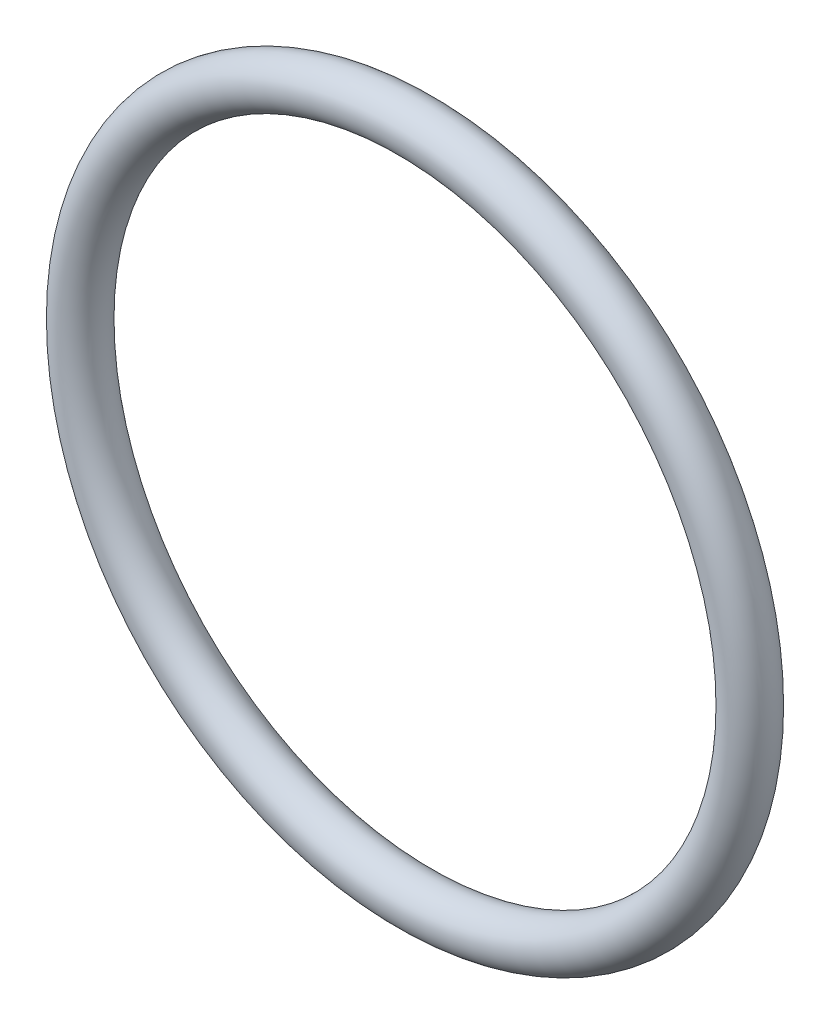
SolidWorks part; units mm, degrees
ref_plane "Plan de face" through (0, 0, 0) normal (0, 0, 1) x (1, 0, 0)
ref_plane "Plan de dessus" through (0, 0, 0) normal (0, 1, 0) x (1, 0, 0)
ref_plane "Plan de droite" through (0, 0, 0) normal (1, 0, 0) x (0, 0, -1)
ref_axis "Axe1" through (0, 0, -88.99) along (0, 0, 1)
sketch "Esquisse1" plane through (0, 0, 0) normal (1, 0, 0) x (0, 0, -1)
  line L0 (0, 28) -> (0, 0) construction
  circle A0 centre (0, 28) radius 2
  dimension "D1" = 4
  dimension "D2" = 28
revolve "Révolution1" add sketch "Esquisse1" angle 360 about axis through (0, 0, -88.99) along (0, 0, 1)
